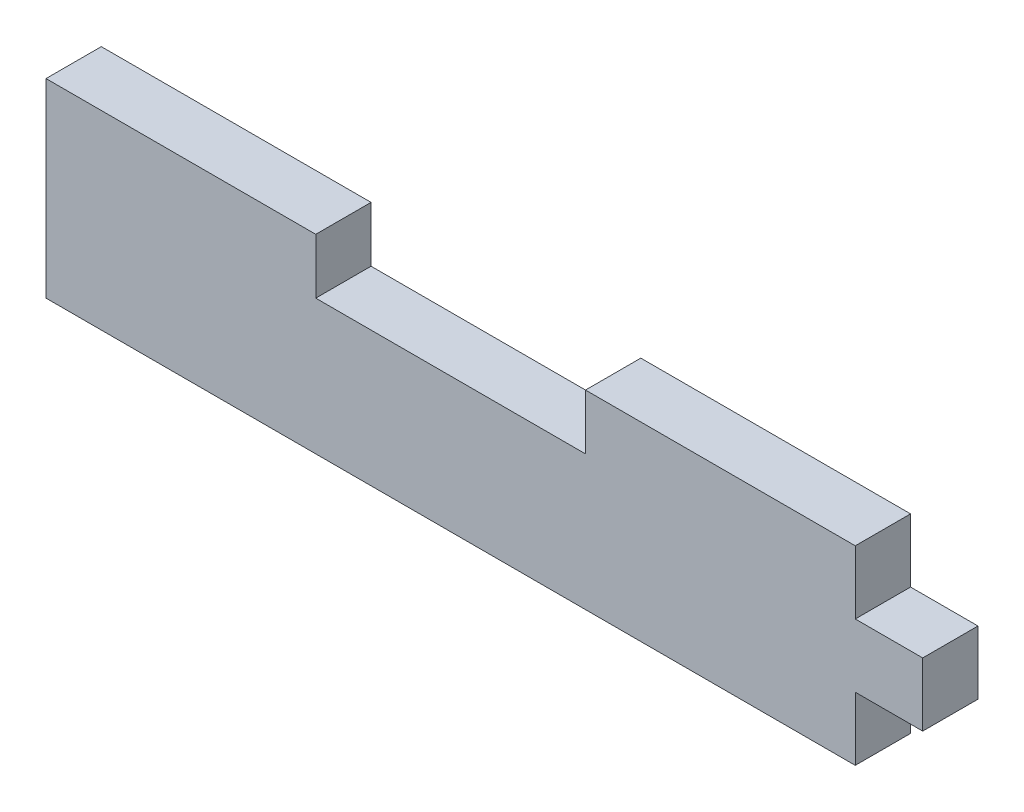
SolidWorks part; units mm, degrees
ref_plane "Front Plane" through (0, 0, 0) normal (0, 0, 1) x (1, 0, 0)
ref_plane "Top Plane" through (0, 0, 0) normal (0, 1, 0) x (1, 0, 0)
ref_plane "Right Plane" through (0, 0, 0) normal (1, 0, 0) x (0, 0, -1)
sketch "Sketch1" plane through (0, 0, 0) normal (0, 0, 1) x (1, 0, 0)
  line L0 (50.8, 17.907) -> (76.2, 17.907)
  line L1 (0, 0) -> (76.2, 0)
  line L2 (0, 0) -> (0, 17.907)
  line L3 (0, 17.907) -> (25.4, 17.907)
  line L4 (76.2, 0) -> (76.2, 5.969)
  line L5 (76.2, 11.938) -> (82.55, 11.938)
  line L7 (76.2, 5.969) -> (82.55, 5.969)
  line L8 (82.55, 11.938) -> (82.55, 5.969)
  line L9 (76.2, 11.938) -> (76.2, 17.907)
  line L10 (25.4, 17.907) -> (25.4, 12.7)
  line L11 (25.4, 12.7) -> (50.8, 12.7)
  line L12 (50.8, 17.907) -> (50.8, 12.7)
  dimension "D1" = 76.2
  dimension "D2" = 12.7
  dimension "D3" = 5.207
  dimension "D4" = 6.35
extrude "Boss-Extrude1" add sketch "Sketch1" along normal blind 5.207
equation "\"mat\" = .205"
equation "\"D3@Sketch1\"= \"mat\""
equation "\"D1@Boss-Extrude1\"= \"mat\""
